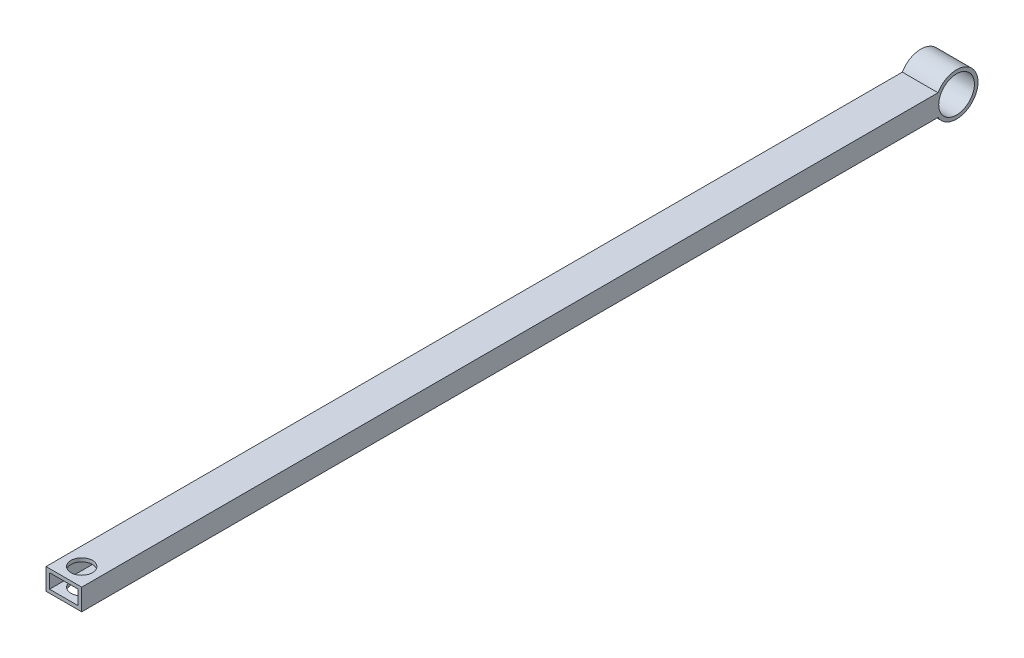
SolidWorks part; units mm, degrees
ref_plane "Front Plane" through (0, 0, 0) normal (0, 0, 1) x (1, 0, 0)
ref_plane "Top Plane" through (0, 0, 0) normal (0, 1, 0) x (1, 0, 0)
ref_plane "Right Plane" through (0, 0, 0) normal (1, 0, 0) x (0, 0, -1)
sketch "Sketch1" plane through (0, 0, 0) normal (0, 0, 1) x (1, 0, 0)
  line L1 (-5, 3) -> (5, 3)
  line L2 (-5, 3) -> (-5, -3)
  line L3 (-5, -3) -> (5, -3)
  line L4 (5, 3) -> (5, -3)
  line L5 (-5, 3) -> (5, -3) construction
  line L6 (-5, -3) -> (5, 3) construction
  point P0 (0, 0)
  dimension "D1" = 6
  dimension "D2" = 10
extrude "Boss-Extrude1" add sketch "Sketch1" along normal blind 250
sketch "Sketch2" plane through (0, 0, 0) normal (0, 0, 1) x (1, 0, 0)
  line L1 (-4, 2) -> (4, 2)
  line L2 (-4, 2) -> (-4, -2)
  line L3 (-4, -2) -> (4, -2)
  line L4 (4, 2) -> (4, -2)
  line L5 (-4, 2) -> (4, -2) construction
  line L6 (-4, -2) -> (4, 2) construction
  point P0 (0, 0)
  dimension "D1" = 4
  dimension "D2" = 8
sketch "Sketch3" plane through (0, 0, 0) normal (0, 1, 0) x (1, 0, 0)
  line L0 (5, -250) -> (5, -240) construction
  line L1 (5, -250) -> (5, 0) construction
  line L2 (5, -237.9657) -> (5, -250) construction
  line L3 (5, -240) -> (-5, -250) construction
  line L7 (-5, -250) -> (5, -250) construction
  line L8 (5, -250) -> (-5, -240) construction
  line L9 (-5, -250) -> (-5, 0) construction
  line L10 (-5, -240) -> (-5, -250) construction
  circle A1 centre (0, -245) radius 3
  dimension "D1" = 10
  dimension "D2" = 6
  dimension "8" = 10
extrude "Cut-Extrude2" cut sketch "Sketch3" against normal blind 249 and the other way blind 249
extrude "Cut-Extrude4" cut sketch "Sketch2" along normal through all both and the other way through all
sketch "Sketch7" plane through (-5, 0, 0) normal (-1, 0, 0) x (0, 0, 1)
  line L1 (0, 0) -> (5, 0) construction
  circle A0 centre (5, 0) radius 6
  dimension "D2" = 12
extrude "Boss-Extrude2" add sketch "Sketch7" against normal blind 10
sketch "Sketch9" plane through (-5, 0, 0) normal (-1, 0, 0) x (0, 0, 1)
  circle A0 centre (5, 0) radius 5
  dimension "D1" = 10
extrude "Cut-Extrude7" cut sketch "Sketch9" against normal through all both and the other way through all
